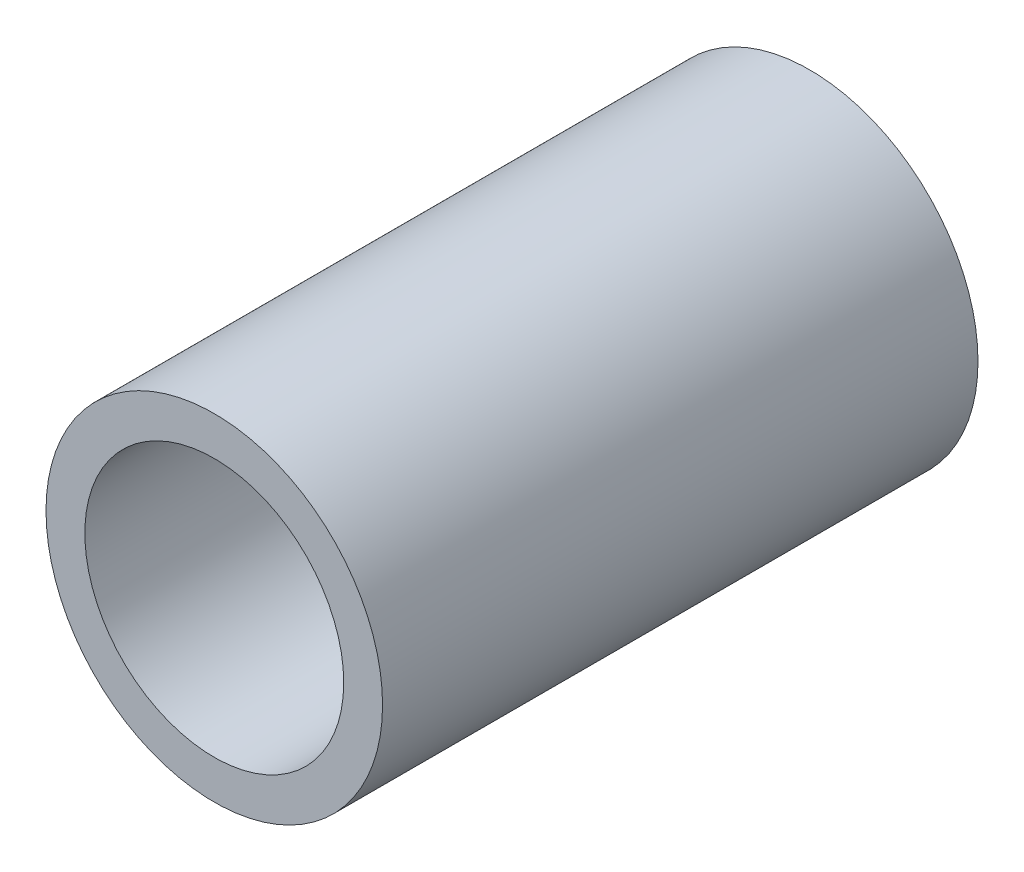
SolidWorks part; units mm, degrees
ref_plane "Front Plane" through (0, 0, 0) normal (0, 0, 1) x (1, 0, 0)
ref_plane "Top Plane" through (0, 0, 0) normal (0, 1, 0) x (1, 0, 0)
ref_plane "Right Plane" through (0, 0, 0) normal (1, 0, 0) x (0, 0, -1)
sketch "Sketch1" plane through (0, 0, 0) normal (0, 0, 1) x (1, 0, 0)
  circle A0 centre (0, 0) radius 15
  circle A1 centre (0, 0) radius 19.5
  point P5 (0, 0)
  dimension "D1" = 30
  dimension "D2" = 39
extrude "Boss-Extrude1" add sketch "Sketch1" along normal mid plane 69
